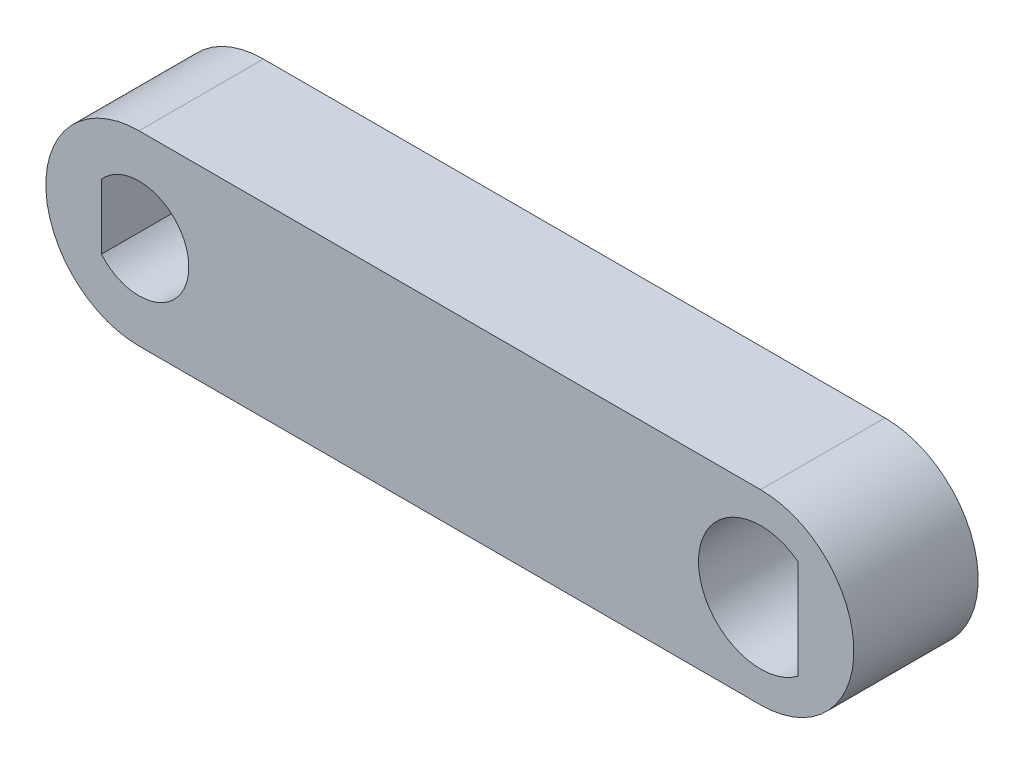
SolidWorks part; units mm, degrees
ref_plane "Ön Düzlem" through (0, 0, 0) normal (0, 0, 1) x (1, 0, 0)
ref_plane "Üst Düzlem" through (0, 0, 0) normal (0, 1, 0) x (1, 0, 0)
ref_plane "Sağ Düzlem" through (0, 0, 0) normal (1, 0, 0) x (0, 0, -1)
sketch "Çizim1" plane through (0, 0, 0) normal (0, 0, 1) x (1, 0, 0)
  line L0 (0, 0) -> (50, 0) construction
  line L1 (0, 7.5) -> (50, 7.5)
  line L2 (0, -7.5) -> (50, -7.5)
  line L3 (53, 4) -> (53, -4)
  line L4 (-3.0298, 2.6116) -> (-3.0298, -2.6116)
  arc A0 (0, 7.5) -> (0, -7.5) centre (0, 0) ccw
  arc A1 (50, -7.5) -> (50, 7.5) centre (50, 0) ccw
  arc A2 (53, 4) -> (53, -4) centre (50, 0) ccw
  arc A3 (-3.0298, -2.6116) -> (-3.0298, 2.6116) centre (0, 0) ccw
  point P3 (25, 0)
  dimension "D2" = 7.5
  dimension "D3" = 10
  dimension "D4" = 8
  dimension "D1" = 50
  dimension "D5" = 3
  dimension "D6" = 4
extrude "Yükseklik-Ekstrüzyon1" add sketch "Çizim1" along normal blind 10
